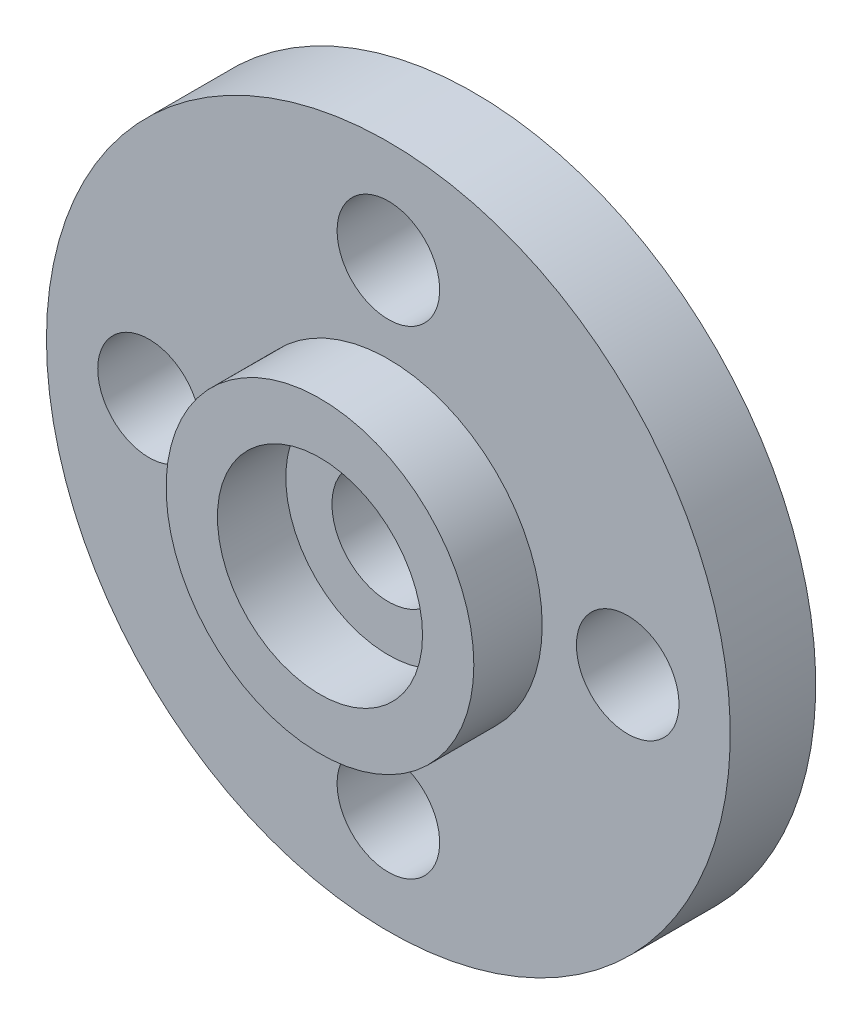
SolidWorks part; units mm, degrees
ref_plane "前视基准面" through (0, 0, 0) normal (0, 0, 1) x (1, 0, 0)
ref_plane "上视基准面" through (0, 0, 0) normal (0, 1, 0) x (1, 0, 0)
ref_plane "右视基准面" through (0, 0, 0) normal (1, 0, 0) x (0, 0, -1)
sketch "草图1" plane through (0, 0, 0) normal (0, 0, 1) x (1, 0, 0)
  circle A0 centre (0, 0) radius 3
  circle A1 centre (0, 0) radius 4.5
  dimension "D1" = 6
  dimension "D2" = 9
extrude "凸台-拉伸1" add sketch "草图1" along normal blind 2
sketch "草图2" plane through (0, 0, 0) normal (0, 0, -1) x (-1, 0, 0)
  circle A0 centre (0, 0) radius 1.65
  circle A1 centre (0, 0) radius 10
  dimension "D1" = 3.3
  dimension "D2" = 20
extrude "凸台-拉伸2" add sketch "草图2" along normal blind 2.5
sketch "草图3" plane through (0, 0, -2.5) normal (0, 0, -1) x (-1, 0, 0)
  line L0 (7, 0) -> (0, 0) construction
  circle A0 centre (7, 0) radius 1.5
  circle A1 centre (0, -7) radius 1.5
  circle A2 centre (-7, 0) radius 1.5
  circle A3 centre (0, 7) radius 1.5
  point P12 (0, 0)
  dimension "D2" = 3
  dimension "D1" = 7
  dimension "D3" = 4
extrude "切除-拉伸1" cut sketch "草图3" against normal blind 2.5
